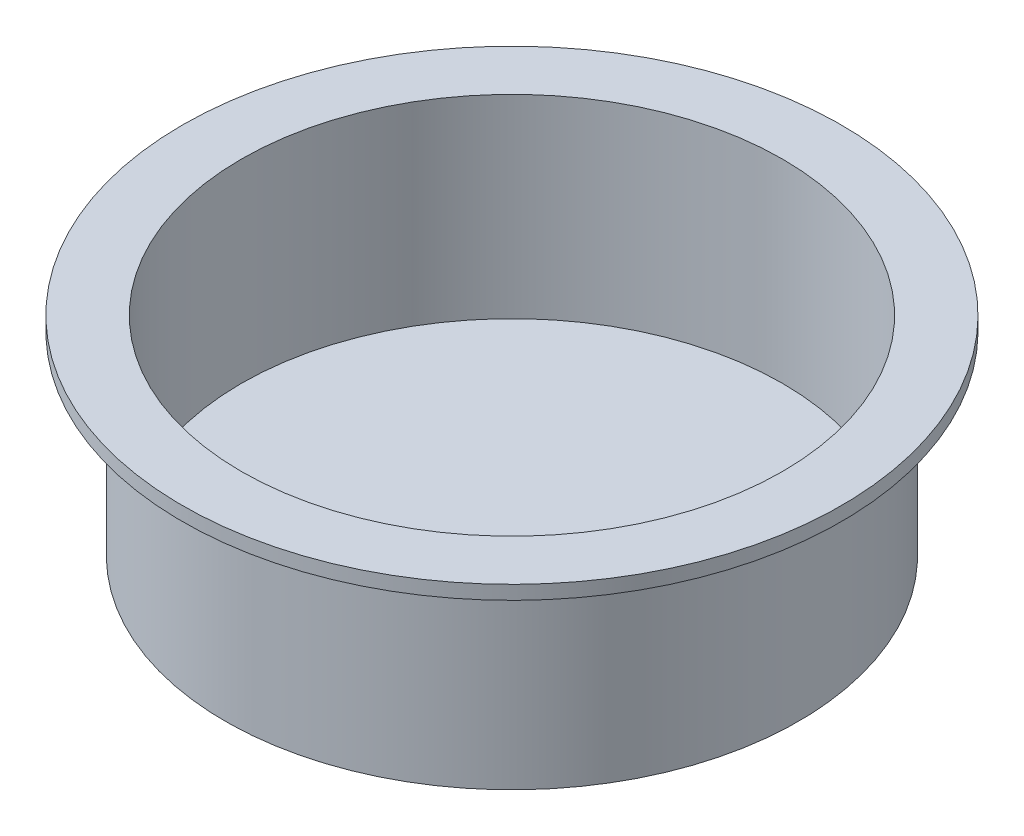
SolidWorks part; units mm, degrees
ref_plane "Front Plane" through (0, 0, 0) normal (0, 0, 1) x (1, 0, 0)
ref_plane "Top Plane" through (0, 0, 0) normal (0, 1, 0) x (1, 0, 0)
ref_plane "Right Plane" through (0, 0, 0) normal (1, 0, 0) x (0, 0, -1)
sketch "Sketch3" plane through (0, 0, 0) normal (0, 0, 1) x (1, 0, 0)
  line L0 (0, 0) -> (26.2509, 0)
  line L1 (26.2509, 0) -> (26.2509, 17.78)
  line L2 (26.2509, 17.78) -> (30.1625, 17.78)
  line L3 (30.1625, 17.78) -> (30.1625, 19.05)
  line L4 (30.1625, 19.05) -> (0, 19.05)
  line L5 (0, 19.05) -> (0, 0)
  dimension "D1" = 26.2509
  dimension "D2" = 30.1625
  dimension "D3" = 1.27
  dimension "D4" = 19.05
revolve "Revolve1" add sketch "Sketch3" angle 360 about L5
sketch "Sketch4" plane through (0, 19.05, 0) normal (0, 1, 0) x (1, 0, 0)
  circle A0 centre (0, 0) radius 24.765
  dimension "D1" = 49.53
extrude "Cut-Extrude1" cut sketch "Sketch4" against normal blind 17.78
